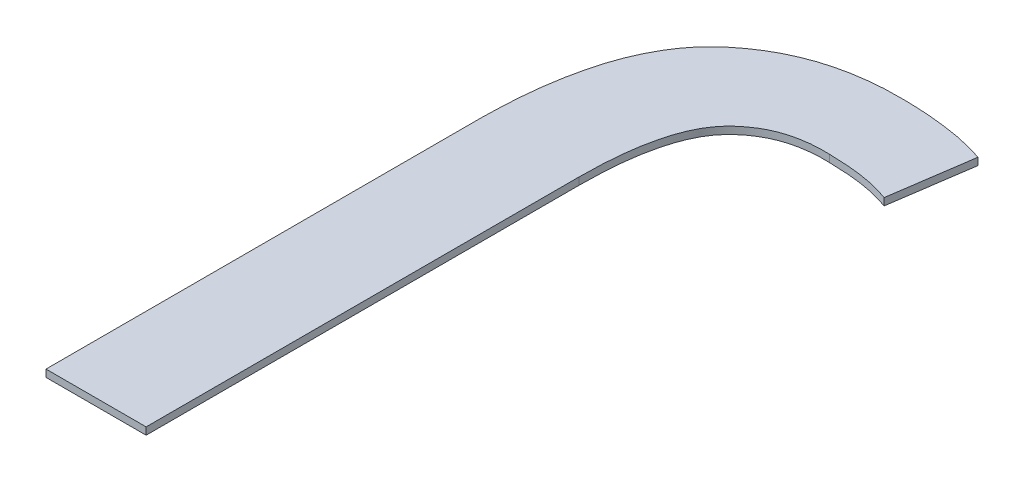
SolidWorks part; units mm, degrees
ref_plane "Спереди" through (0, 0, 0) normal (0, 0, 1) x (1, 0, 0)
ref_plane "Сверху" through (0, 0, 0) normal (0, 1, 0) x (1, 0, 0)
ref_plane "Справа" through (0, 0, 0) normal (1, 0, 0) x (0, 0, -1)
sketch "Эскиз1" plane through (0, 0, 0) normal (0, 1, 0) x (1, 0, 0)
  text T0 "<r180>J</r>" font "@Adobe Heiti Std R" height 0.54
extrude "Бобышка-Вытянуть1" add sketch "Эскиз1" along normal blind 0.006
